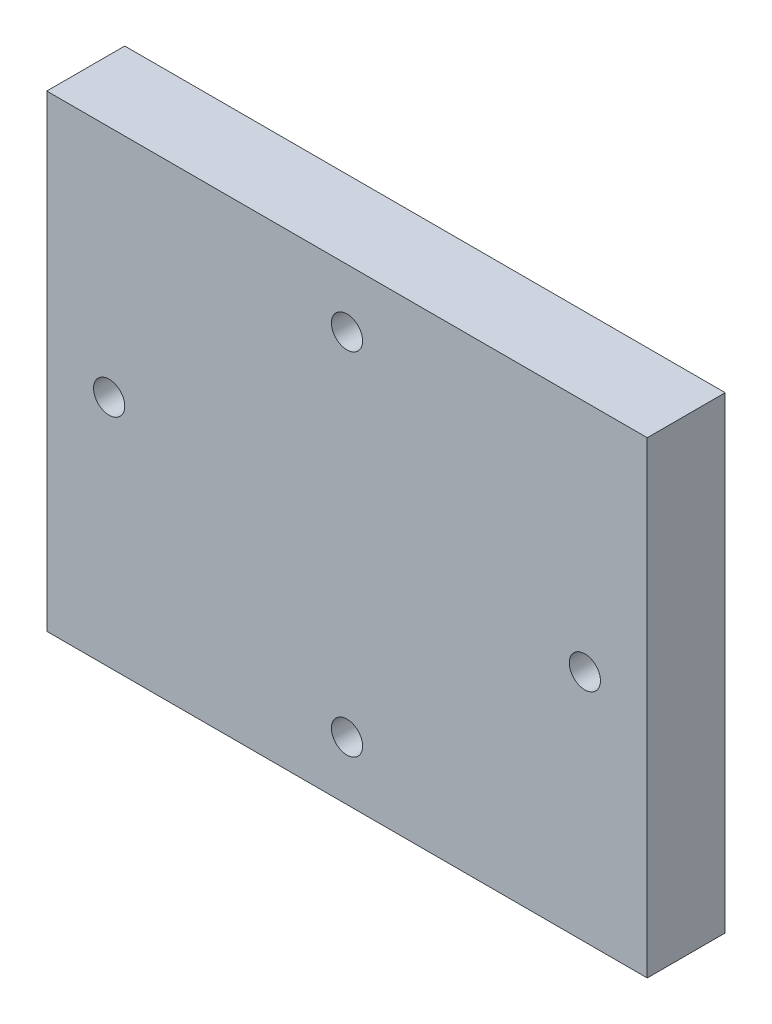
SolidWorks part; units mm, degrees
ref_plane "前视基准面" through (0, 0, 0) normal (0, 0, 1) x (1, 0, 0)
ref_plane "上视基准面" through (0, 0, 0) normal (0, 1, 0) x (1, 0, 0)
ref_plane "右视基准面" through (0, 0, 0) normal (1, 0, 0) x (0, 0, -1)
sketch "草图1" plane through (0, 0, 0) normal (0, 0, 1) x (1, 0, 0)
  line L0 (-30.7697, 30.7697) -> (46.2303, 30.7697)
  line L1 (46.2303, 30.7697) -> (46.2303, -29.2303)
  line L2 (46.2303, -29.2303) -> (-30.7697, -29.2303)
  line L3 (-30.7697, -29.2303) -> (-30.7697, 30.7697)
  line L4 (7.7303, 30.7697) -> (7.7303, 23.2697) construction
  line L5 (46.2303, 0.7697) -> (-30.7697, 0.7697) construction
  line L6 (46.2303, 0.7697) -> (38.2303, 0.7697) construction
  line L7 (-30.7697, 0.7697) -> (-22.7697, 0.7697) construction
  line L8 (7.7303, 23.2697) -> (7.7303, -21.7303) construction
  circle A0 centre (7.7303, 23.2697) radius 2
  circle A1 centre (7.7303, -21.7303) radius 2
  circle A2 centre (38.2303, 0.7697) radius 2
  circle A3 centre (-22.7697, 0.7697) radius 2
  dimension "D4" = 4
  dimension "D6" = 4
  dimension "D8" = 4
  dimension "D1" = 77
  dimension "D2" = 60
  dimension "D3" = 7.5
  dimension "D5" = 8
  dimension "D7" = 8
extrude "凸台-拉伸1" add sketch "草图1" along normal blind 10
